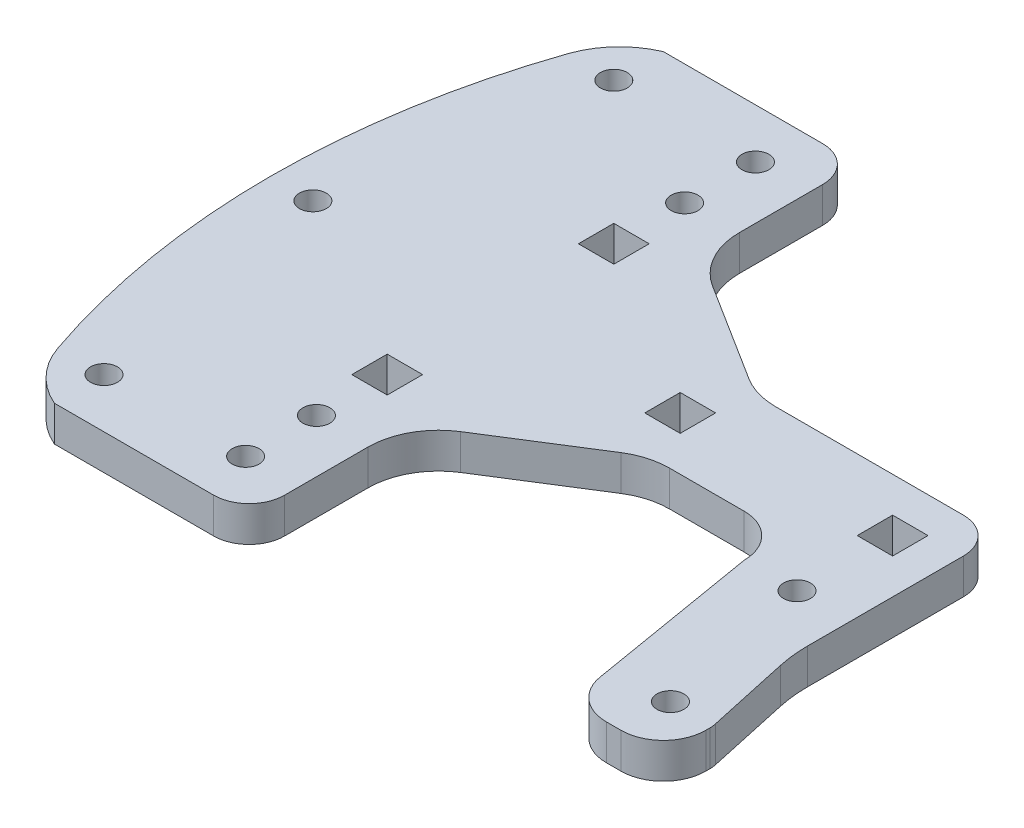
SolidWorks part; units mm, degrees
ref_plane "Front Plane" through (0, 0, 0) normal (0, 0, 1) x (1, 0, 0)
ref_plane "Top Plane" through (0, 0, 0) normal (0, 1, 0) x (1, 0, 0)
ref_plane "Right Plane" through (0, 0, 0) normal (1, 0, 0) x (0, 0, -1)
sketch "Sketch1" plane through (0, 0, 0) normal (0, 1, 0) x (1, 0, 0)
  line L0 (-7.4512, 9.6917) -> (-7.4512, -27.7227) construction
  line L1 (-37.9392, 19.2167) -> (-4.2762, 19.2167)
  line L3 (-37.9392, 0.1667) -> (-27.3876, 0.1667)
  line L4 (2.0738, 12.8667) -> (2.0738, 5.2467)
  line L5 (-10.6262, 12.8667) -> (-4.2762, 12.8667)
  line L6 (-10.6262, 12.8667) -> (-10.6262, 6.5167)
  line L7 (-10.6262, 6.5167) -> (-4.2762, 6.5167)
  line L8 (-4.2762, 12.8667) -> (-4.2762, 6.5167)
  line L9 (-10.6262, 12.8667) -> (-4.2762, 6.5167) construction
  line L10 (-10.6262, 6.5167) -> (-4.2762, 12.8667) construction
  line L11 (-7.4512, 9.6917) -> (-119.0552, 9.6917) construction
  line L12 (-45.5512, 30.0117) -> (-45.5512, -10.6283) construction
  line L13 (-48.7262, 6.5167) -> (-42.3762, 6.5167)
  line L14 (-48.7262, 6.5167) -> (-48.7262, 12.8667)
  line L15 (-48.7262, 12.8667) -> (-42.3762, 12.8667)
  line L16 (-42.3762, 6.5167) -> (-42.3762, 12.8667)
  line L17 (-48.7262, 6.5167) -> (-42.3762, 12.8667) construction
  line L18 (-48.7262, 12.8667) -> (-42.3762, 6.5167) construction
  line L19 (-45.5512, 30.0117) -> (-101.948, 30.0117) construction
  line L20 (-44.7125, -1.7903) -> (-62.3286, -12.897)
  line L21 (-45.5512, 9.6917) -> (-77.7802, 30.0117) construction
  line L22 (-74.6052, -7.4533) -> (-74.6052, -13.8033)
  line L23 (-77.7802, 30.0117) -> (-77.7802, 63.0449) construction
  line L24 (-80.9552, 26.8367) -> (-74.6052, 26.8367)
  line L25 (-80.9552, 26.8367) -> (-80.9552, 33.1867)
  line L26 (-80.9552, 33.1867) -> (-74.6052, 33.1867)
  line L27 (-74.6052, 26.8367) -> (-74.6052, 33.1867)
  line L28 (-80.9552, 26.8367) -> (-74.6052, 33.1867) construction
  line L29 (-80.9552, 33.1867) -> (-74.6052, 26.8367) construction
  line L34 (-80.9552, -13.8033) -> (-74.6052, -13.8033)
  line L35 (-80.9552, -7.4533) -> (-80.9552, -13.8033)
  line L36 (-80.9552, -7.4533) -> (-74.6052, -7.4533)
  line L37 (-44.7125, 21.1737) -> (-62.3286, 32.2804)
  line L38 (-68.2552, -38.5683) -> (-68.2552, -23.64)
  line L39 (-28.2812, 10.8139) -> (-72.3616, -25.7394) construction
  line L40 (-28.2812, 10.8139) -> (-72.3616, 38.6061) construction
  line L43 (-119.0552, 30.0117) -> (-119.0552, 57.9517) construction
  line L45 (-103.1802, 64.3017) -> (-74.6052, 64.3017)
  line L46 (-68.2552, 57.9517) -> (-68.2552, 43.0234)
  line L48 (-119.0552, -10.6283) -> (-119.0552, -38.5683) construction
  line L49 (-103.1802, -44.9183) -> (-74.6052, -44.9183)
  line L50 (-45.5512, 9.6917) -> (-78.8469, -17.9186) construction
  line L51 (-119.0552, 30.0117) -> (-119.0552, -10.6283) construction
  line L52 (-77.7802, 55.4117) -> (-118.3701, 55.4117) construction
  line L53 (-77.7802, -36.0283) -> (-119.0552, -36.0283) construction
  line L54 (2.0738, 5.2467) -> (2.0738, -15.1114)
  line L60 (-80.9552, -10.6283) -> (-74.6052, -10.6283) construction
  line L61 (-77.7802, -10.6283) -> (-77.7802, -41.0344) construction
  line L62 (2.6575, -20.5256) -> (5.923, -35.4932)
  line L63 (-27.3876, 0.1667) -> (-24.5537, 0.1667)
  line L64 (-16.9337, -7.4533) -> (-11.6961, -38.5634)
  line L65 (6.0398, -36.576) -> (6.0398, -37.2983)
  line L66 (-1.5802, -44.9183) -> (-4.1819, -44.9183)
  arc A1 (-68.2552, -23.64) -> (-62.3286, -12.897) centre (-55.5552, -23.64) cw
  circle A2 centre (-77.7802, 42.7117) radius 2.413
  circle A3 centre (-77.7802, 55.4117) radius 2.413
  arc A4 (-68.2552, 43.0234) -> (-62.3286, 32.2804) centre (-55.5552, 43.0234) ccw
  circle A5 centre (-77.7802, -23.3283) radius 2.413
  circle A6 centre (-77.7802, -36.0283) radius 2.413
  arc A7 (-119.0552, -38.5683) -> (-112.7052, -44.9183) centre (-112.7052, -38.5683) ccw construction
  arc A8 (-74.6052, -44.9183) -> (-68.2552, -38.5683) centre (-74.6052, -38.5683) ccw
  arc A9 (-74.6052, 64.3017) -> (-68.2552, 57.9517) centre (-74.6052, 57.9517) cw
  arc A10 (-112.7052, 64.3017) -> (-119.0552, 57.9517) centre (-112.7052, 57.9517) ccw construction
  arc A11 (-44.7125, -1.7903) -> (-37.9392, 0.1667) centre (-37.9392, -12.5333) cw
  arc A12 (-37.9392, 19.2167) -> (-44.7125, 21.1737) centre (-37.9392, 31.9167) cw
  arc A14 (2.0738, 12.8667) -> (-4.2762, 19.2167) centre (-4.2762, 12.8667) ccw
  circle A15 centre (-111.4352, 9.6917) radius 2.413
  circle A16 centre (-103.1802, 55.4117) radius 2.413
  circle A18 centre (-103.1802, -36.0283) radius 2.413
  circle A20 centre (-1.5802, -36.0283) radius 2.413
  circle A23 centre (-7.4512, -7.4533) radius 2.413
  arc A29 (-4.1819, -44.9183) -> (-11.6961, -38.5634) centre (-4.1819, -37.2983) cw
  arc A30 (-16.9337, -7.4533) -> (-24.5537, 0.1667) centre (-24.5537, -7.4533) ccw
  arc A31 (6.0398, -37.2983) -> (-1.5802, -44.9183) centre (-1.5802, -37.2983) cw
  arc A32 (2.0738, -15.1114) -> (2.6575, -20.5256) centre (27.4738, -15.1114) ccw
  arc A33 (6.0398, -36.576) -> (5.923, -35.4932) centre (0.9598, -36.576) ccw
  arc A34 (-111.4352, 55.4117) -> (-111.4352, -36.0283) centre (21.9148, 9.6917) ccw
  arc A35 (-111.4352, -36.0283) -> (-103.1802, -44.9183) centre (-97.3026, -31.1828) ccw
  arc A36 (-111.4352, 55.4117) -> (-103.1802, 64.3017) centre (-97.3026, 50.5662) cw
  point P0 (-77.7802, 42.7117)
  point P4 (-7.4512, 9.6917)
  point P11 (-45.5512, 9.6917)
  point P20 (-45.5512, 9.6917)
  point P59 (-119.0552, -44.9183)
  point P62 (-68.2552, -44.9183)
  point P65 (-68.2552, 64.3017)
  point P68 (-119.0552, 64.3017)
  point P99 (5.2488, -24.6633)
  point P110 (6.0398, -36.0283)
  dimension "D9" = 12.7
  dimension "D17" = 8.89
  dimension "D21" = 12.7
  dimension "D12" = 6.35
  dimension "D16" = 12.7
  dimension "D22" = 7.62
  dimension "D23" = 7.62
  dimension "D26" = 4.826
  dimension "D27" = 4.826
  dimension "D28" = 4.826
  dimension "D29" = 4.826
  dimension "D30" = 4.826
  dimension "D31" = 76.2
  dimension "D32" = 7.62
  dimension "D33" = 12.7
  dimension "D34" = 7.62
  dimension "D35" = 25.4
  dimension "D36" = 5.08
  dimension "D1" = 6.35
  dimension "D2" = 6.35
  dimension "D3" = 6.35
  dimension "D4" = 6.35
  dimension "D5" = 38.1
  dimension "D6" = 6.35
  dimension "D7" = 6.35
  dimension "D8" = 6.35
  dimension "D10" = 56.3968
  dimension "D11" = 38.1
  dimension "D13" = 6.35
  dimension "D14" = 6.35
  dimension "D15" = 12.7
  dimension "D19" = 6.35
  dimension "D20" = 38.1
  dimension "D24" = 25.4
  dimension "D25" = 25.4
  dimension "D18" = 10.16
extrude "Boss-Extrude1" add sketch "Sketch1" along normal blind 6.35
